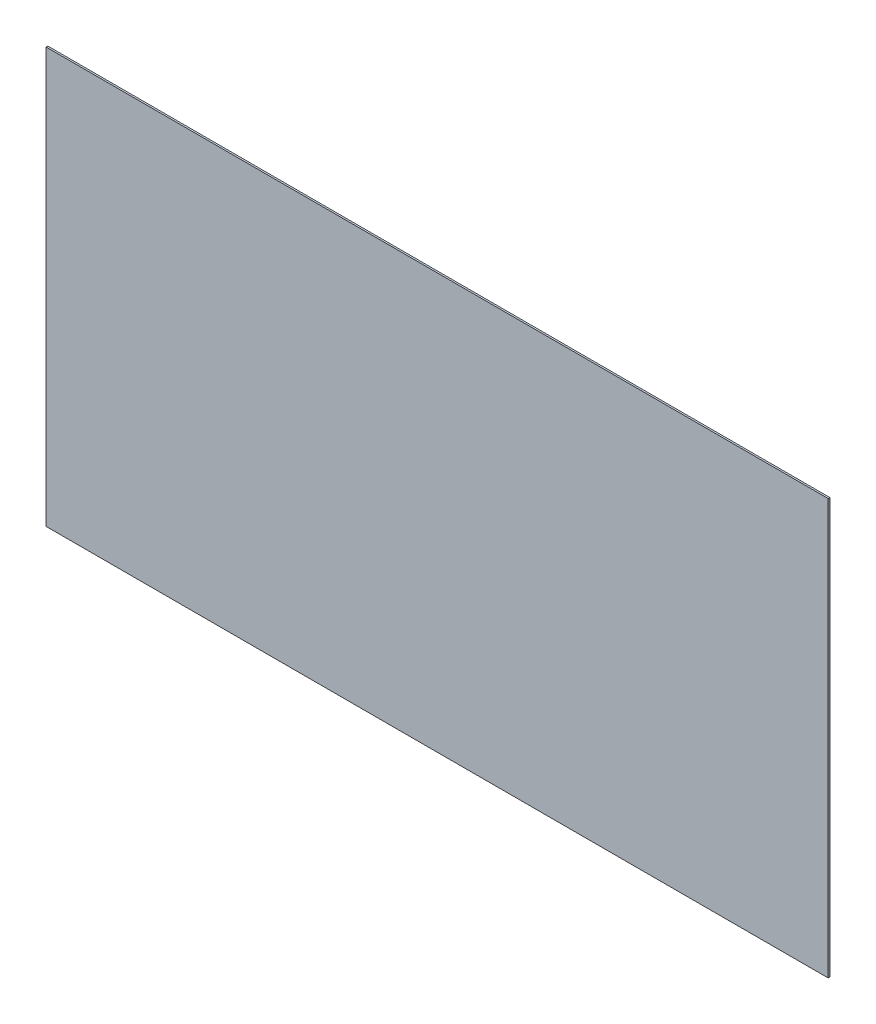
SolidWorks part; units mm, degrees
ref_plane "Front Plane" through (0, 0, 0) normal (0, 0, 1) x (1, 0, 0)
ref_plane "Top Plane" through (0, 0, 0) normal (0, 1, 0) x (1, 0, 0)
ref_plane "Right Plane" through (0, 0, 0) normal (1, 0, 0) x (0, 0, -1)
sketch "Sketch1" plane through (0, 0, 0) normal (0, 0, 1) x (1, 0, 0)
  line L1 (0, 0) -> (717.804, 0)
  line L2 (0, 0) -> (0, 381)
  line L3 (0, 381) -> (717.804, 381)
  line L4 (717.804, 0) -> (717.804, 381)
  dimension "D1" = 381
  dimension "D2" = 717.804
extrude "Boss-Extrude1" add sketch "Sketch1" along normal blind 1.5875
